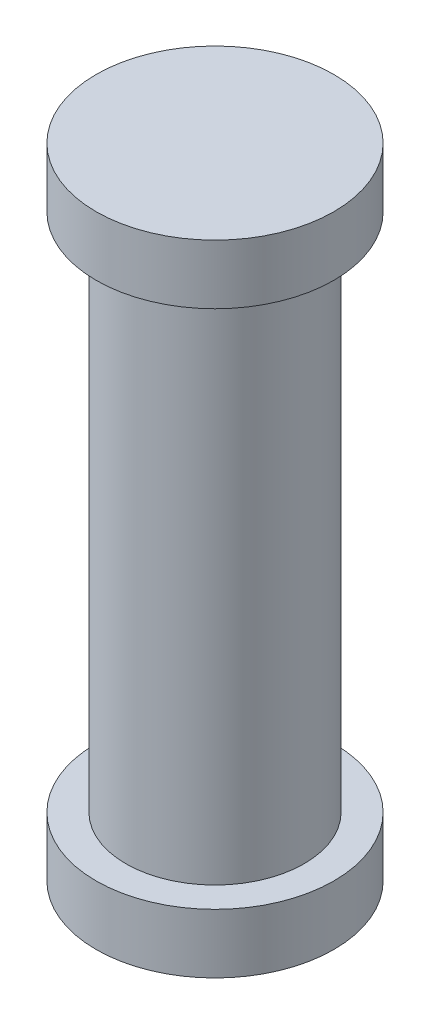
SolidWorks part; units mm, degrees
ref_plane "Front Plane" through (0, 0, 0) normal (0, 0, 1) x (1, 0, 0)
ref_plane "Top Plane" through (0, 0, 0) normal (0, 1, 0) x (1, 0, 0)
ref_plane "Right Plane" through (0, 0, 0) normal (1, 0, 0) x (0, 0, -1)
sketch "Sketch1" plane through (0, 0, 0) normal (0, 1, 0) x (1, 0, 0)
  circle A0 centre (0, 0) radius 1.6
extrude "Boss-Extrude1" add sketch "Sketch1" along normal blind 0.8
sketch "Sketch2" plane through (0, 0.8, 0) normal (0, 1, 0) x (1, 0, 0)
  circle A0 centre (0, 0) radius 1.2
extrude "Boss-Extrude2" add sketch "Sketch2" along normal blind 7
sketch "Sketch3" plane through (0, 7.8, 0) normal (0, 1, 0) x (1, 0, 0)
  circle A0 centre (0, 0) radius 1.6
extrude "Boss-Extrude3" add sketch "Sketch3" along normal blind 0.8
